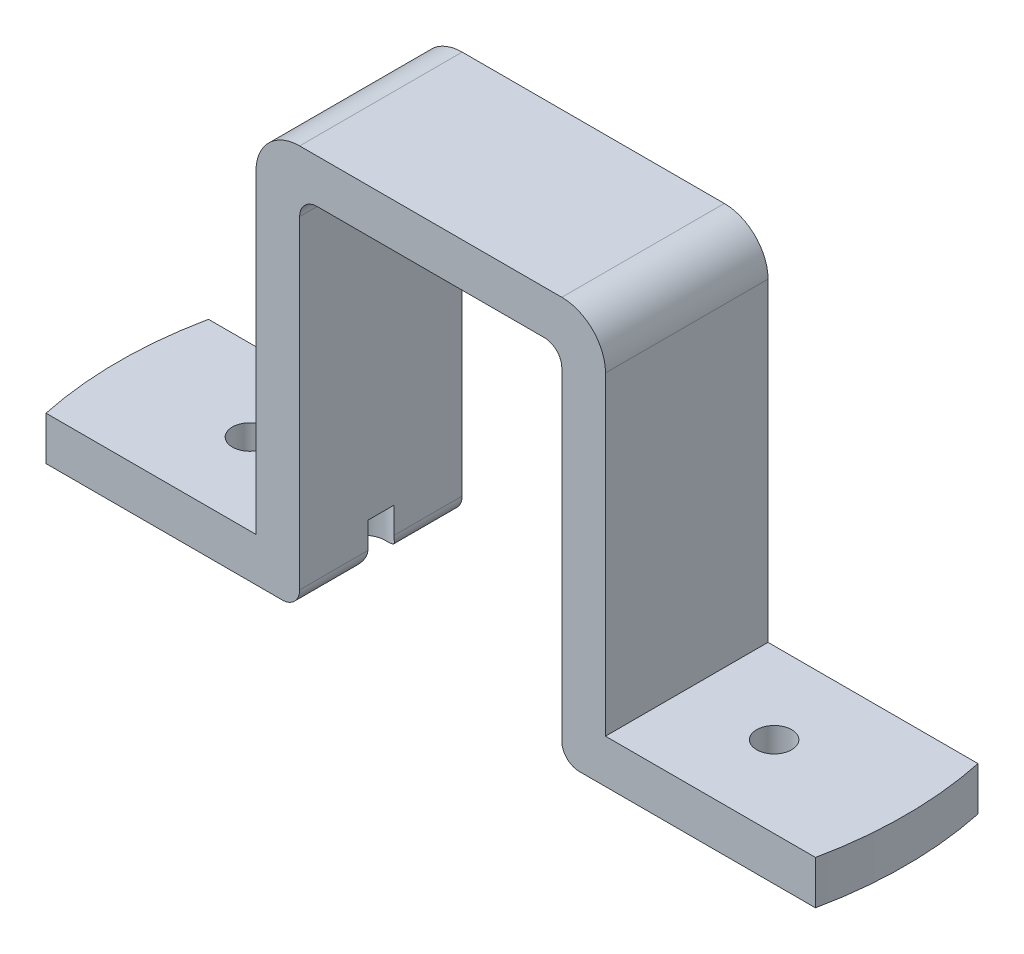
SolidWorks part; units mm, degrees
ref_plane "Front Plane" through (0, 0, 0) normal (0, 0, 1) x (1, 0, 0)
ref_plane "Top Plane" through (0, 0, 0) normal (0, 1, 0) x (1, 0, 0)
ref_plane "Right Plane" through (0, 0, 0) normal (1, 0, 0) x (0, 0, -1)
sketch "Sketch1" plane through (0, 0, 0) normal (0, 0, 1) x (1, 0, 0)
  line L0 (0, 0) -> (30, 0)
  line L1 (30, 0) -> (30, 41)
  line L2 (30, 41) -> (60, 41)
  line L3 (60, 41) -> (60, 0)
  line L4 (60, 0) -> (90, 0)
  line L5 (0, 5) -> (25, 5)
  line L6 (25, 5) -> (25, 46)
  line L7 (25, 46) -> (65, 46)
  line L8 (65, 46) -> (65, 5)
  line L9 (65, 5) -> (90, 5)
  line L10 (0, 5) -> (0, 0)
  line L11 (0, 0) -> (0.2363, -0.5696)
  line L12 (90, 5) -> (90, 0)
  dimension "D1" = 90
  dimension "D3" = 41
  dimension "D4" = 30
  dimension "D5" = 5
extrude "Boss-Extrude1" add sketch "Sketch1" along normal blind 18.6 contours L12 L9 L8 L7 L6 L5 L10 L0 L1 L2 L3 L4
sketch "Sketch2" plane through (0, 5, 0) normal (0, 1, 0) x (1, 0, 0)
  line L0 (45, 0) -> (45, -18.6) construction
  line L1 (25, 0) -> (65, 0) construction
  line L2 (25, -18.6) -> (65, -18.6) construction
  line L3 (0, -18.6) -> (0, 0) construction
  circle A0 centre (75, -9.3) radius 2
  circle A1 centre (15, -9.3) radius 2
  circle A2 centre (28, -9.3) radius 2.5
  circle A3 centre (62, -9.3) radius 2.5
  point P12 (0, -9.3)
  point P18 (45, -9.3)
  dimension "D1" = 4
  dimension "D2" = 4
  dimension "D5" = 5
  dimension "D6" = 5
  dimension "D3" = 30
  dimension "D4" = 30
  dimension "D7" = 17
  dimension "D8" = 17
extrude "Cut-Extrude1" cut sketch "Sketch2" against normal blind 10
ref_plane "Plane1" through (0, 56, 0) normal (0, 1, 0) x (1, 0, 0)
sketch "Sketch3" plane through (0, 46, 0) normal (0, 1, 0) x (1, 0, 0)
  line L0 (45, 0) -> (45, -18.6) construction
  line L1 (25, 0) -> (65, 0) construction
  line L2 (25, -18.6) -> (65, -18.6) construction
  circle A0 centre (45, -9.3) radius 45
  circle A1 centre (45, -9.3) radius 50
  dimension "D1" = 90
  dimension "D2" = 5
extrude "Cut-Extrude2" cut sketch "Sketch3" against normal blind 60
fillet "Fillet1" radius 5 1 edges at (25, 46, 9.3)
fillet "Fillet2" radius 5 1 edges at (65, 46, 9.3)
fillet "Fillet3" radius 2 4 edges at (30, 0, 14.7) (60, 0, 14.7) (60, 41, 9.3) (30, 41, 9.3)
fillet "Fillet4" radius 2 2 edges at (30, 0, 3.9) (60, 0, 3.9)
